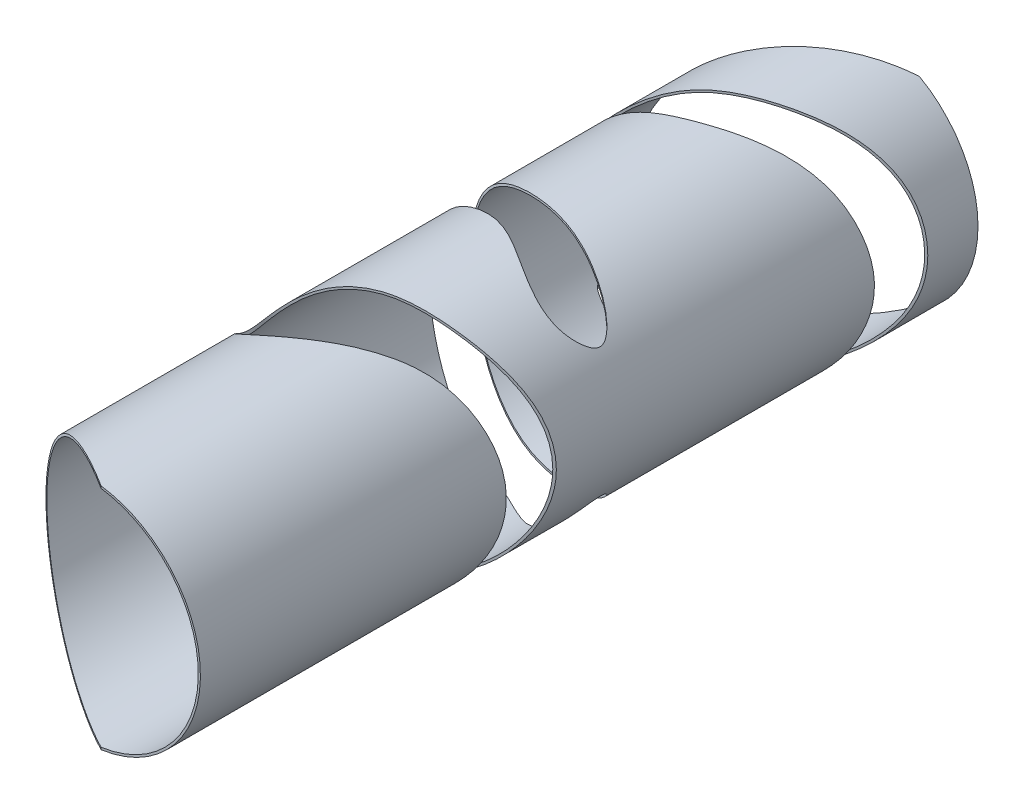
SolidWorks part; units mm, degrees
material "S 235"
ref_plane "Plan de face" through (0, 0, 0) normal (0, 0, 1) x (1, 0, 0)
ref_plane "Plan de dessus" through (0, 0, 0) normal (0, 1, 0) x (1, 0, 0)
ref_plane "Plan de droite" through (0, 0, 0) normal (1, 0, 0) x (0, 0, -1)
sketch "Esquisse1" plane through (0, 0, 0) normal (0, 0, 1) x (1, 0, 0)
  circle A0 centre (0, 0) radius 535.1001
extrude "Extru.-Mince1" add sketch "Esquisse1" against normal blind 3674 thin
sketch "Esquisse2" plane through (0, 0, 0) normal (0, 1, 0) x (1, 0, 0)
  line L0 (373.6081, 3744.0615) -> (-1281.5156, 2642.3296)
  line L1 (-1281.5156, 2642.3296) -> (-1778.118, 3368.7995)
  line L2 (-1778.118, 3368.7995) -> (-119.2471, 4238.5009)
  line L3 (-119.2471, 4238.5009) -> (360.1782, 3735.122)
  line L4 (-995.757, 622.2983) -> (259.5336, -106.7358)
  line L5 (259.5336, -106.7358) -> (-792.9792, -362.622)
  line L6 (-792.9792, -362.622) -> (-995.757, 622.2983)
  spline S0 degree 3 poles (645.3594, 3223.4684) (717.2757, 3605.2881) (201.567, 3192.1197) (-99.2123, 3073.5061) (-288.253, 2982.6438) (-492.5744, 2827.7116) (-158.0161, 2841.2721) (81.8877, 2904.2605) (382.8438, 3112.8281) (645.3594, 3223.4684) (717.2757, 3605.2881) (201.567, 3192.1197) knots -0.321468 -0.147743 -0.055436 0 0.204661 0.336786 0.439004 0.483058 0.545667 0.678532 0.852257 0.944564 1 1.204661 1.336786 1.439004 only from (668.8763, 3418.3587) to (668.8763, 3418.3587)
  spline S1 degree 3 poles (-766.9673, 2238.2391) (-960.1912, 2566.0563) (-385.3914, 2279.3913) (-71.8656, 2207.2122) (241.3485, 2154.9821) (491.1699, 2020.037) (344.1506, 1757.9565) (31.8539, 2017.4407) (-290.8451, 2066.0928) (-547.2861, 2171.2768) (-766.9673, 2238.2391) (-960.1912, 2566.0563) (-385.3914, 2279.3913) knots -0.245271 -0.124153 -0.069971 0 0.139485 0.2906 0.413218 0.478079 0.515299 0.657922 0.754729 0.875847 0.930029 1 1.139485 1.2906 1.413218 only from (-854.8495, 2431.972) to (-854.8495, 2431.972)
  spline S2 degree 3 poles (730.0992, 1480.1987) (1014.9962, 2059.0886) (343.893, 1480.1316) (27.1138, 1501.3098) (-555.0099, 1313.1239) (-225.8194, 845.1321) (298.3993, 1396.9521) (730.0992, 1480.1987) (1014.9962, 2059.0886) (343.893, 1480.1316) knots -0.473247 -0.258129 -0.075998 0 0.146033 0.351881 0.462785 0.526753 0.741871 0.924002 1 1.146033 1.351881 1.462785 only from (906.4911, 1886.3191) to (906.4911, 1886.3191)
extrude "Enlèv. mat.-Extru.1" cut sketch "Esquisse2" against normal mid plane 3028 contours L3 L2 L1 L0 | S0 | S1 | S2 | L6 L5 L4
